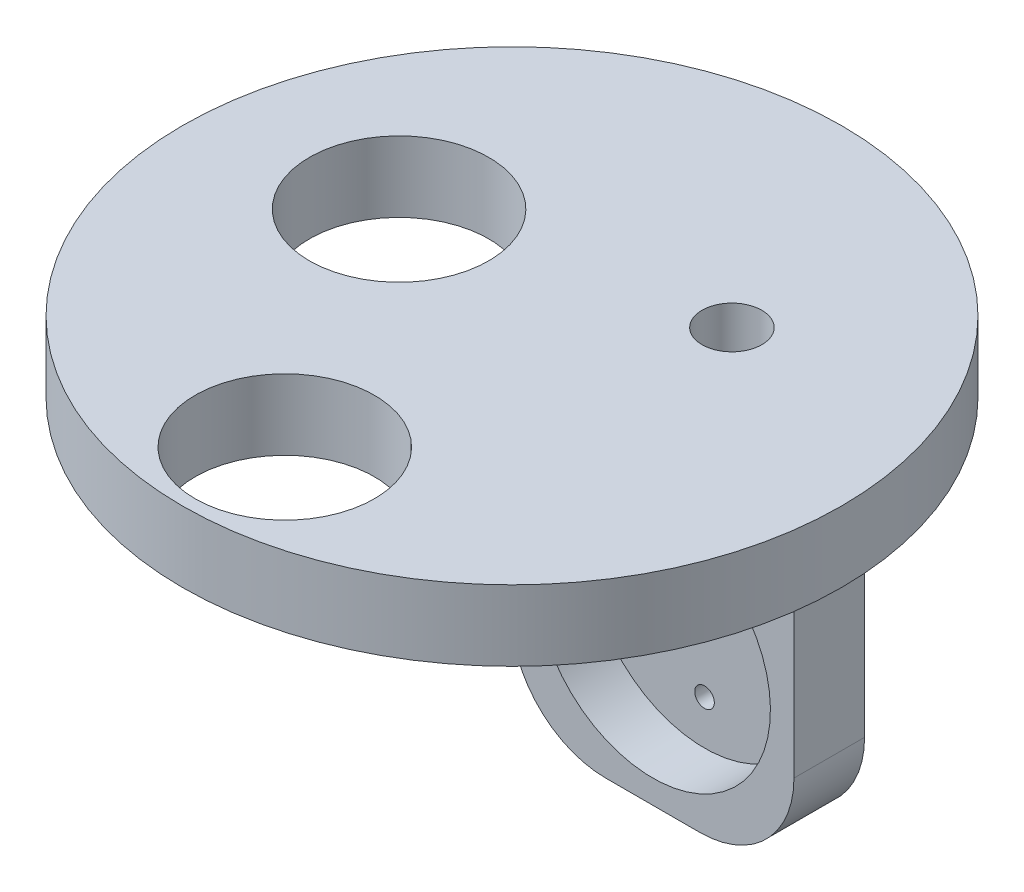
SolidWorks part; units mm, degrees
ref_plane "Front Plane" through (0, 0, 0) normal (0, 0, 1) x (1, 0, 0)
ref_plane "Top Plane" through (0, 0, 0) normal (0, 1, 0) x (1, 0, 0)
ref_plane "Right Plane" through (0, 0, 0) normal (1, 0, 0) x (0, 0, -1)
sketch "Sketch1" plane through (0, 0, 0) normal (0, 0, 1) x (1, 0, 0)
  line L1 (-15, -22.5) -> (15, -22.5)
  line L2 (-15, -22.5) -> (-15, 22.5)
  line L3 (-15, 22.5) -> (15, 22.5)
  line L4 (15, -22.5) -> (15, 22.5)
  line L5 (0, 22.5) -> (0, -22.5) construction
  line L6 (-15, 0) -> (15, 0) construction
  point P0 (0, 0)
  dimension "D1" = 30
  dimension "D2" = 45
extrude "Boss-Extrude1" add sketch "Sketch1" along normal blind 7.5
sketch "Sketch2" plane through (0, 0, 7.5) normal (0, 0, 1) x (1, 0, 0)
  line L5 (-15, -22.5) -> (15, -22.5) construction
  circle A0 centre (0, -7.5) radius 12.5
  point P6 (0, -22.5)
  dimension "D2" = 25
  dimension "D1" = 15
extrude "Cut-Extrude1" cut sketch "Sketch2" against normal offset from surface (5.5 mm away) 2 up to face at (0, 0, 0)
sketch "Sketch4" plane through (0, 0, 2) normal (0, 0, 1) x (1, 0, 0)
  circle A0 centre (0, -7.5) radius 7.8 construction
  circle A1 centre (0, -7.5) radius 12.5 construction
  circle A2 centre (0, -15.3) radius 1.04
  circle A3 centre (6.755, -3.6) radius 1.04
  circle A4 centre (-6.755, -3.6) radius 1.04
  circle A5 centre (0, -7.5) radius 10 construction
  dimension "D1" = 11.43
  dimension "D2" = 11.43
  dimension "D3" = 11.43
  dimension "D4" = 20
  dimension "D5" = 1.16
extrude "Cut-Extrude2" cut sketch "Sketch4" against normal up to next
fillet "Fillet1" radius 10 2 edges at (15, -22.5, 3.75) (-15, -22.5, 3.75)
sketch "Sketch6" plane through (0, 0, 7.5) normal (0, 0, 1) x (1, 0, 0)
  line L1 (-1.75, 27) -> (1.75, 27)
  line L2 (-1.75, 27) -> (-1.75, -7.5)
  line L3 (-1.75, -7.5) -> (1.75, -7.5)
  line L4 (1.75, 27) -> (1.75, -7.5)
  line L5 (0, -7.5) -> (0, 27) construction
  line L6 (-1.75, 9.75) -> (1.75, 9.75) construction
  circle A2 centre (0, -7.5) radius 12.5 construction
  circle A3 centre (0, -7.5) radius 12.5 construction
  point P0 (0, 9.75)
  dimension "D1" = 3.5
  dimension "D2" = 22
extrude "Cut-Extrude3" cut sketch "Sketch6" against normal up to next
sketch "Sketch9" plane through (0, 22.5, 0) normal (0, 1, 0) x (1, 0, 0)
  circle A0 centre (0, -22.4499) radius 35
  circle A1 centre (0, -22.4499) radius 27 construction
  dimension "D1" = 70
  dimension "D2" = 8
extrude "Boss-Extrude3" add sketch "Sketch9" along normal blind 7.5 contours A0
sketch "Sketch10" plane through (0, 30, 0) normal (0, 1, 0) x (1, 0, 0)
  circle A0 centre (0, -46.5851) radius 9.525
  circle A1 centre (-15.8138, -18.6296) radius 9.525
  circle A2 centre (12.7539, -11.8444) radius 3.175
  circle A3 centre (0, -46.5851) radius 9.525 construction
extrude "Cut-Extrude4" cut sketch "Sketch10" against normal up to next
